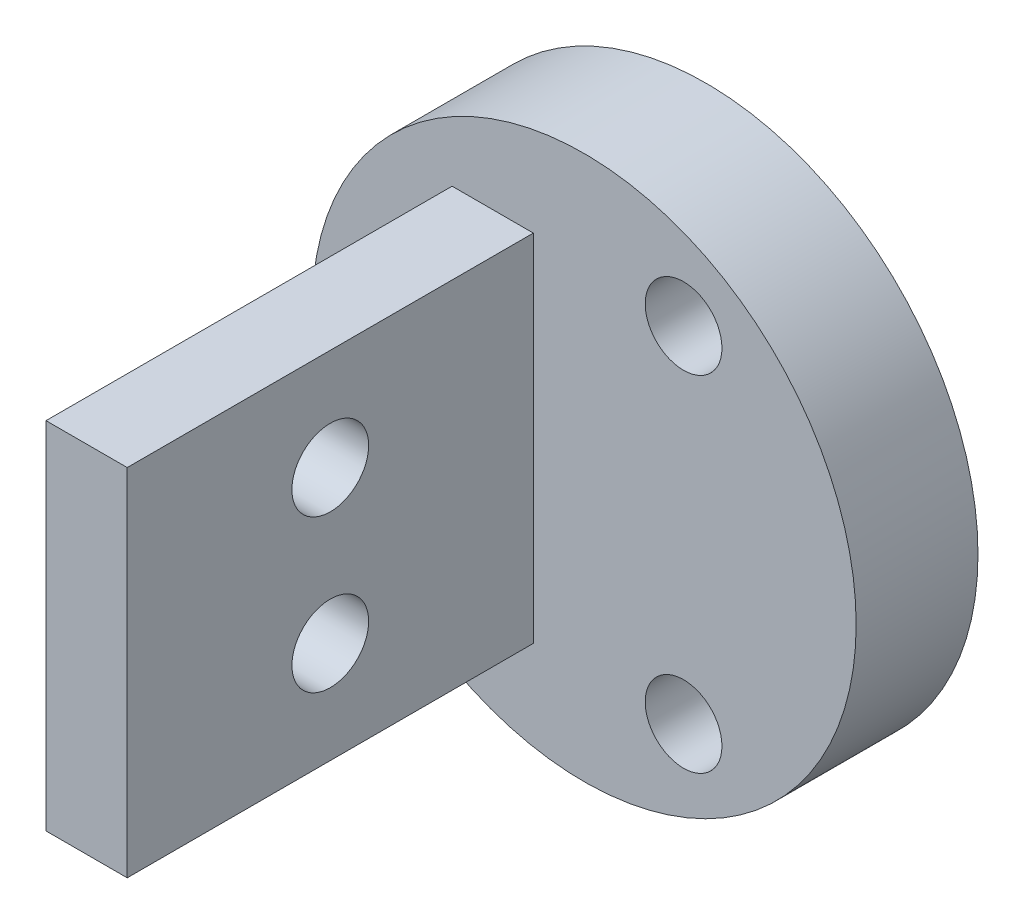
SolidWorks part; units mm, degrees
ref_plane "Front Plane" through (0, 0, 0) normal (0, 0, 1) x (1, 0, 0)
ref_plane "Top Plane" through (0, 0, 0) normal (0, 1, 0) x (1, 0, 0)
ref_plane "Right Plane" through (0, 0, 0) normal (1, 0, 0) x (0, 0, -1)
sketch "Sketch2" plane through (0, 0, 0) normal (0, 0, 1) x (1, 0, 0)
  circle A0 centre (0, 0) radius 8.509
  dimension "D1" = 17.018
extrude "Boss-Extrude1" add sketch "Sketch2" along normal blind 3.81
ref_plane "Plane1" through (0, 0, 3.81) normal (0, 0, 1) x (1, 0, 0)
sketch "Sketch3" plane through (0, 0, 3.81) normal (0, 0, 1) x (1, 0, 0)
  line L0 (-8.509, 0) -> (8.509, 0) construction
  circle A0 centre (0, 0) radius 6.223 construction
  circle A2 centre (0, 0) radius 8.509 construction
  circle A3 centre (-6.223, 0) radius 1.143
  circle A4 centre (3.1115, 5.3893) radius 1.143
  circle A5 centre (3.1115, -5.3893) radius 1.143
  point P16 (0, 0)
  dimension "D1" = 12.446
  dimension "D2" = 2.286
  dimension "D4" = 5.3893
  dimension "D5" = 3.1115
  dimension "D3" = 3
sketch "Sketch4" plane through (0, 0, 3.81) normal (0, 0, 1) x (1, 0, 0)
  line L1 (-4.1275, 5.5562) -> (-1.5875, 5.5562)
  line L2 (-4.1275, 5.5562) -> (-4.1275, -5.5562)
  line L3 (-4.1275, -5.5562) -> (-1.5875, -5.5562)
  line L4 (-1.5875, 5.5562) -> (-1.5875, -5.5562)
  dimension "D1" = 2.54
  dimension "D2" = 11.1125
  dimension "D3" = 1.5875
  dimension "D4" = 5.5562
extrude "Boss-Extrude2" add sketch "Sketch4" along normal blind 12.7
sketch "Sketch5" plane through (-1.5875, 0, 0) normal (1, 0, 0) x (0, 0, -1)
  line L0 (-16.51, -5.5562) -> (-16.51, 5.5562) construction
  line L1 (-16.51, -5.5562) -> (-3.81, -5.5562) construction
  line L2 (-16.51, 5.5562) -> (-3.81, 5.5562) construction
  circle A0 centre (-10.16, 2.3813) radius 1.143
  circle A1 centre (-10.16, -2.3812) radius 1.143
  dimension "D1" = 2.286
  dimension "D2" = 2.286
  dimension "D3" = 6.35
  dimension "D4" = 6.35
  dimension "D5" = 3.175
  dimension "D6" = 3.175
hole_wizard "M2 Clearance Hole1" positions "Sketch6" profile "Sketch7" hole size "M2" standard "ANSI Metric" end condition through all
sketch "Sketch6" plane through (0, 0, 3.81) normal (0, 0, 1) x (1, 0, 0)
  point P0 (-6.223, 0)
  point P3 (3.1115, 5.3893)
  point P6 (3.1115, -5.3893)
sketch "Sketch7" plane through (-6.223, 0, 3.81) normal (1, 0, 0) x (0, -1, 0)
  line L0 (0, 0) -> (0, 3.81)
  line L1 (0, 3.81) -> (1.2, 3.81)
  line L2 (1.2, 3.81) -> (1.2, 0)
  line L5 (1.2, 0) -> (0, 0)
  line L11 (0, -6.35) -> (0, 107.95) construction
  dimension "Thru Hole Dia." = 2.4
  dimension "Thru Hole Depth" = 3.81
hole_wizard "M2 Clearance Hole2" positions "Sketch8" profile "Sketch9" hole size "M2" standard "ANSI Metric" end condition through all
sketch "Sketch8" plane through (-1.5875, 0, 0) normal (1, 0, 0) x (0, 0, -1)
  point P0 (-10.16, -2.3812)
  point P3 (-10.16, 2.3813)
sketch "Sketch9" plane through (-1.5875, -2.3812, 10.16) normal (0, 1, 0) x (0, 0, -1)
  line L0 (0, 0) -> (0, 6.9215)
  line L1 (0, 6.9215) -> (1.2, 6.9215)
  line L2 (1.2, 6.9215) -> (1.2, 0)
  line L5 (1.2, 0) -> (0, 0)
  line L11 (0, -6.35) -> (0, 107.95) construction
  dimension "Thru Hole Dia." = 2.4
  dimension "Thru Hole Depth" = 6.9215
